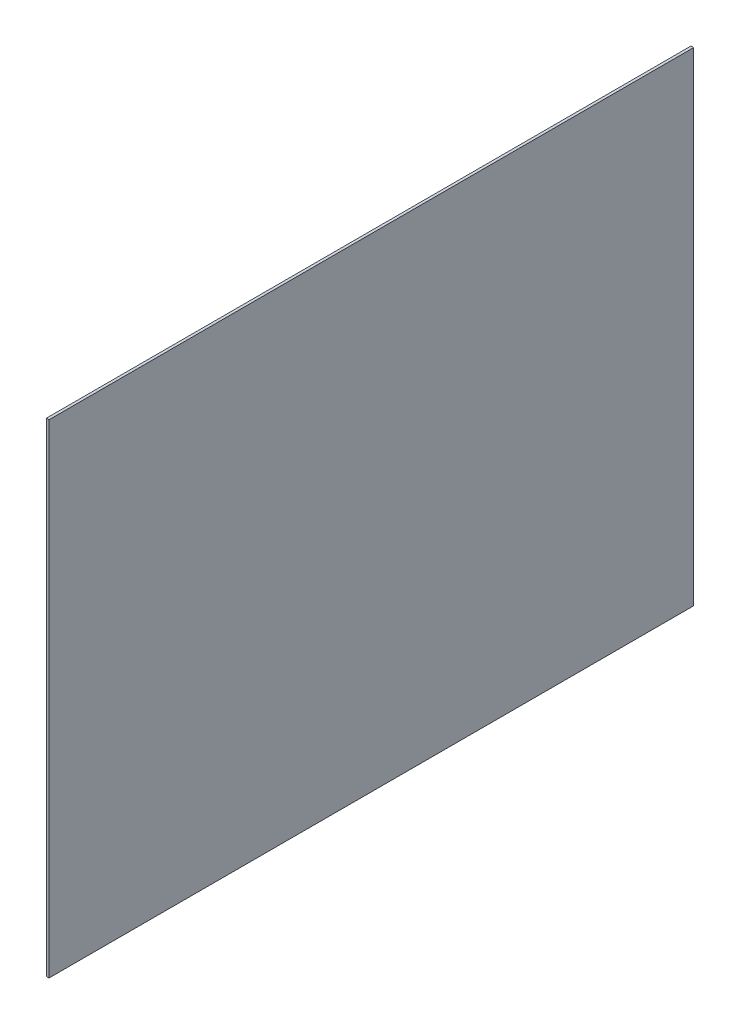
SolidWorks part; units mm, degrees
ref_plane "Front Plane" through (0, 0, 0) normal (0, 0, 1) x (1, 0, 0)
ref_plane "Top Plane" through (0, 0, 0) normal (0, 1, 0) x (1, 0, 0)
ref_plane "Right Plane" through (0, 0, 0) normal (1, 0, 0) x (0, 0, -1)
sketch "Sketch1" plane through (0, 0, 0) normal (1, 0, 0) x (0, 0, -1)
  line L1 (-304.8, 228.6) -> (304.8, 228.6)
  line L2 (-304.8, 228.6) -> (-304.8, -228.6)
  line L3 (-304.8, -228.6) -> (304.8, -228.6)
  line L4 (304.8, 228.6) -> (304.8, -228.6)
  line L5 (-304.8, 228.6) -> (304.8, -228.6) construction
  line L6 (-304.8, -228.6) -> (304.8, 228.6) construction
  point P0 (0, 0)
  dimension "D1" = 457.2
  dimension "D2" = 609.6
extrude "Boss-Extrude1" add sketch "Sketch1" along normal blind 2.54
